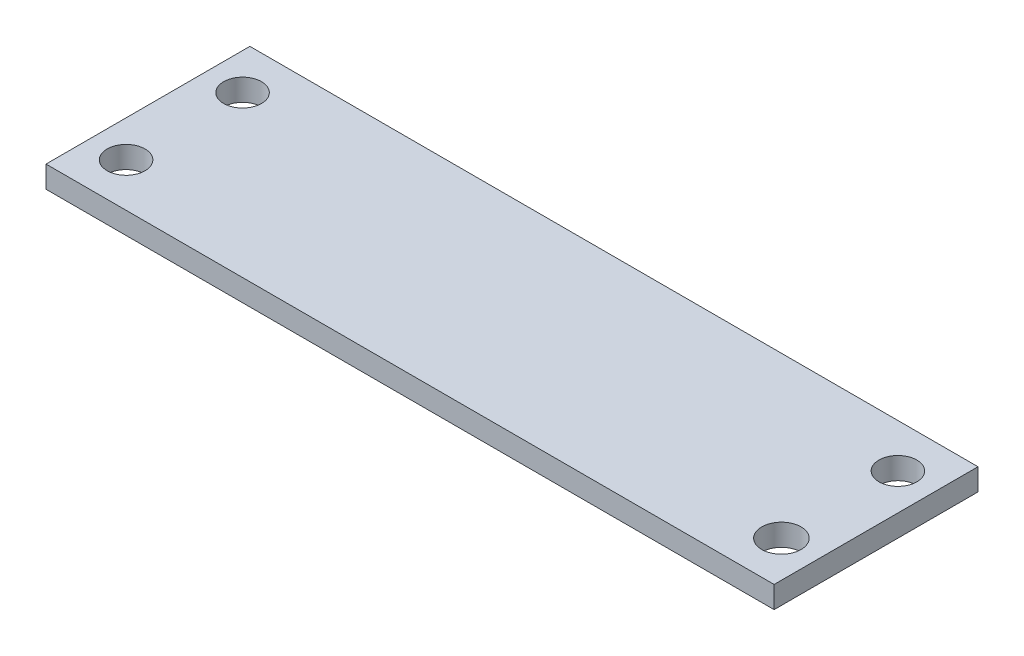
SolidWorks part; units mm, degrees
ref_plane "前视基准面" through (0, 0, 0) normal (0, 0, 1) x (1, 0, 0)
ref_plane "上视基准面" through (0, 0, 0) normal (0, 1, 0) x (1, 0, 0)
ref_plane "右视基准面" through (0, 0, 0) normal (1, 0, 0) x (0, 0, -1)
sketch "草图1" plane through (0, 0, 0) normal (0, 1, 0) x (1, 0, 0)
  line L0 (0, 0) -> (22.5, 0) construction
  line L1 (0, 0) -> (-22.5, 0) construction
  line L2 (0, 0) -> (0, 11) construction
  line L3 (0, 11) -> (25, 11)
  line L4 (25, 11) -> (25, -3)
  line L5 (25, -3) -> (-25, -3)
  line L6 (-25, -3) -> (-25, 11)
  line L7 (-25, 11) -> (0, 11)
  line L8 (-22.5, 0) -> (-22.5, 8) construction
  line L9 (22.5, 0) -> (22.5, 8) construction
  circle A0 centre (22.5, 0) radius 1.35
  circle A1 centre (-22.5, 0) radius 1.3
  circle A2 centre (-22.5, 8) radius 1.3
  circle A3 centre (22.5, 8) radius 1.3
extrude "凸台-拉伸1" add sketch "草图1" along normal blind 1.5
